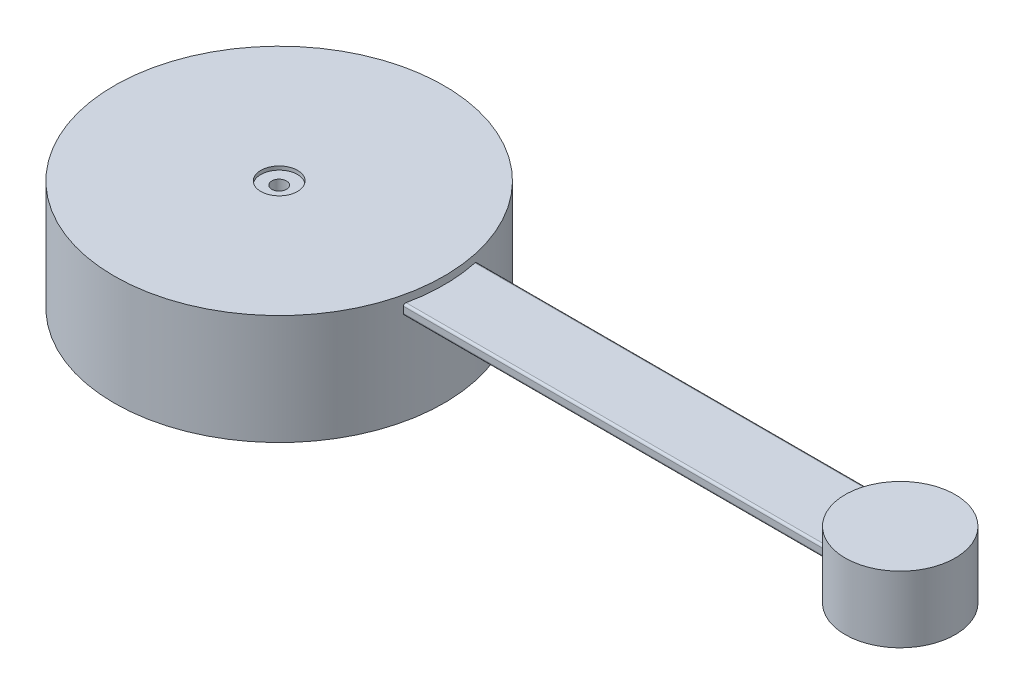
SolidWorks part; units mm, degrees
ref_plane "前视基准面" through (0, 0, 0) normal (0, 0, 1) x (1, 0, 0)
ref_plane "上视基准面" through (0, 0, 0) normal (0, 1, 0) x (1, 0, 0)
ref_plane "右视基准面" through (0, 0, 0) normal (1, 0, 0) x (0, 0, -1)
sketch "草图1" plane through (0, 0, 0) normal (0, 1, 0) x (1, 0, 0)
  line L0 (0, 0) -> (85.9214, 0) construction
  circle A0 centre (0, 0) radius 22.5
  circle A1 centre (85.9214, 0) radius 7.5
  dimension "D1" = 45
  dimension "D2" = 15
extrude "凸台-拉伸1" add sketch "草图1" along normal mid plane 15
sketch "草图3" plane through (0, 7.5, 0) normal (0, 1, 0) x (1, 0, 0)
  line L0 (0, 0) -> (84.7, 0) construction
  circle A0 centre (84.7, 0) radius 7.5
  dimension "D1" = 15
  dimension "D2" = 84.7
extrude "凸台-拉伸2" add sketch "草图3" along normal mid plane 15 separate body
sketch "草图4" plane through (0, 0, 0) normal (1, 0, 0) x (0, 0, -1)
  line L1 (-11.2405, 18.1819) -> (12.2401, 18.1819)
  line L2 (-11.2405, 18.1819) -> (-11.2405, 9.0528)
  line L3 (-11.2405, 9.0528) -> (12.2401, 9.0528)
  line L4 (12.2401, 18.1819) -> (12.2401, 9.0528)
extrude "切除-拉伸2" cut sketch "草图4" along normal through all
ref_plane "基准面1" through (86.82, 0, 0) normal (1, 0, 0) x (0, 0, -1)
sketch "草图5" plane through (86.82, 0, 0) normal (1, 0, 0) x (0, 0, -1)
  line L2 (5, 5.0297) -> (-5, 5.0297)
  line L3 (5, 5.0297) -> (5, 6.4664)
  line L4 (5, 6.4664) -> (-5, 6.4664)
  line L5 (-5, 5.0297) -> (-5, 6.4664)
  line L6 (5, 5.0297) -> (-5, 6.4664) construction
  line L7 (5, 6.4664) -> (-5, 5.0297) construction
  point P2 (0, 5.7481)
  dimension "D1" = 10
  dimension "D2" = 1.4367
extrude "凸台-拉伸3" add sketch "草图5" against normal up to body separate body
sketch "草图6" plane through (0, 7.5, 0) normal (0, 1, 0) x (1, 0, 0)
  circle A0 centre (0, 0) radius 2.5
  dimension "D1" = 5
extrude "切除-拉伸3" cut sketch "草图6" against normal blind 0.5
sketch "草图7" plane through (0, 7, 0) normal (0, 1, 0) x (1, 0, 0)
  circle A0 centre (0, 0) radius 1
extrude "切除-拉伸4" cut sketch "草图7" against normal blind 3
fillet "圆角1" radius 0.3 4 edges at (50.5236, 5.0297, -5) (50.5236, 6.4664, -5) (50.5236, 5.0297, 5) (50.5236, 6.4664, 5)
